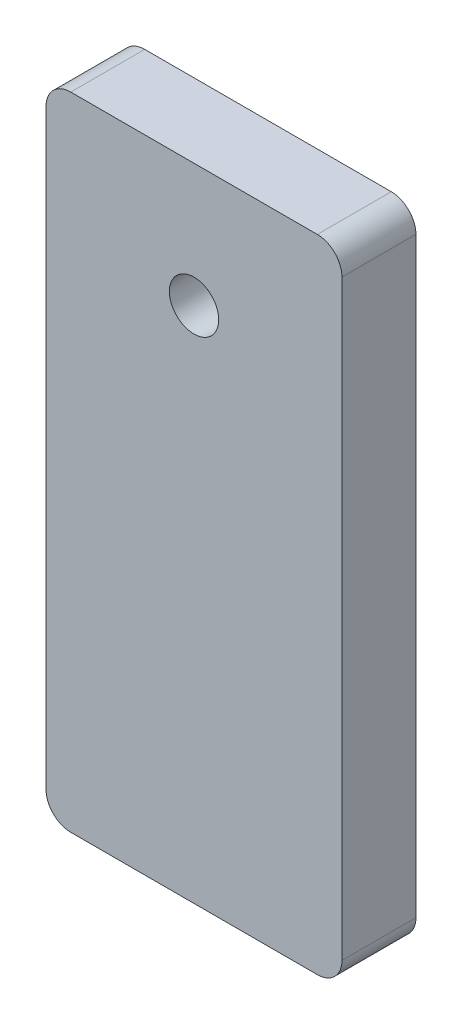
SolidWorks part; units mm, degrees
ref_plane "Front Plane" through (0, 0, 0) normal (0, 0, 1) x (1, 0, 0)
ref_plane "Top Plane" through (0, 0, 0) normal (0, 1, 0) x (1, 0, 0)
ref_plane "Right Plane" through (0, 0, 0) normal (1, 0, 0) x (0, 0, -1)
sketch "Sketch3" plane through (0, 0, 0) normal (0, 0, 1) x (1, 0, 0)
  line L16 (-5, 0) -> (5, 0)
  line L17 (-6, -1) -> (-6, -25)
  line L18 (-5, -26) -> (5, -26)
  line L19 (6, -1) -> (6, -25)
  circle A5 centre (0, -5) radius 1
  arc A6 (5, 0) -> (6, -1) centre (5, -1) cw
  arc A7 (-5, 0) -> (-6, -1) centre (-5, -1) ccw
  arc A8 (5, -26) -> (6, -25) centre (5, -25) ccw
  arc A9 (-6, -25) -> (-5, -26) centre (-5, -25) ccw
  point P4 (0, 0)
  point P9 (6, 0)
  point P14 (6, -26)
  point P17 (-6, -26)
  dimension "D4" = 1
  dimension "D3" = 2
  dimension "D6" = 1
  dimension "D1" = 26
  dimension "D2" = 5
  dimension "D5" = 12
extrude "Boss-Extrude1" add sketch "Sketch3" along normal blind 3
